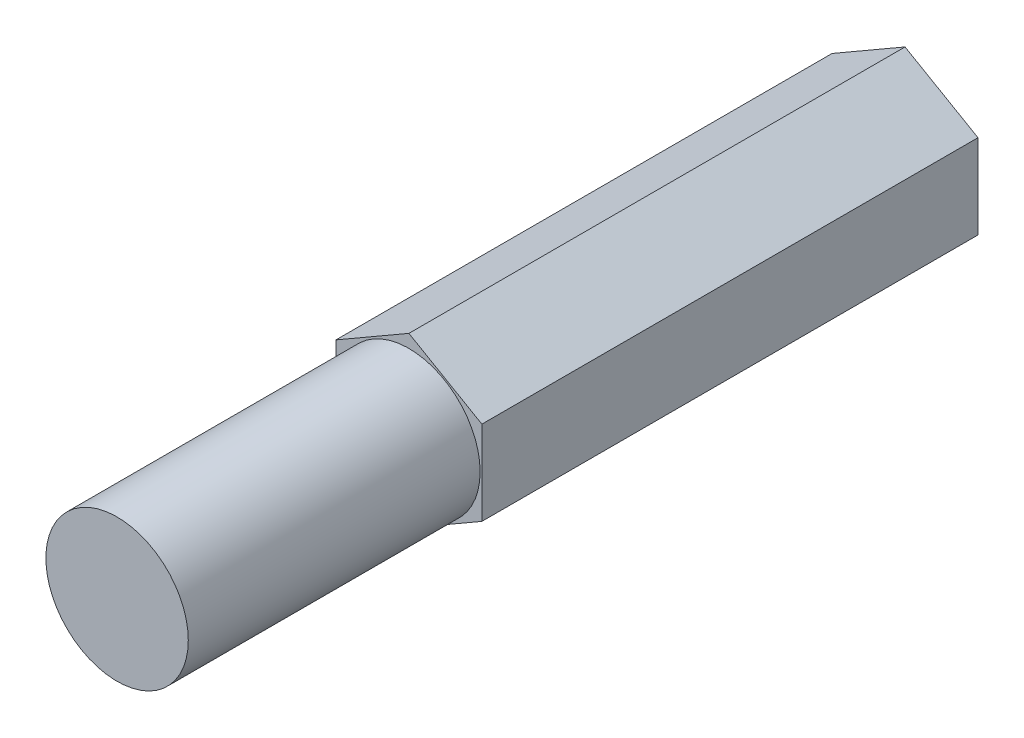
SolidWorks part; units mm, degrees
ref_plane "Front Plane" through (0, 0, 0) normal (0, 0, 1) x (1, 0, 0)
ref_plane "Top Plane" through (0, 0, 0) normal (0, 1, 0) x (1, 0, 0)
ref_plane "Right Plane" through (0, 0, 0) normal (1, 0, 0) x (0, 0, -1)
sketch "Sketch1" plane through (0, 0, 0) normal (0, 0, 1) x (1, 0, 0)
  circle A0 centre (0, 0) radius 3.0988
  dimension "D1" = 6.1976
extrude "Boss-Extrude1" add sketch "Sketch1" against normal blind 12.7
sketch "Sketch2" plane through (0, 0, -12.7) normal (0, 0, -1) x (-1, 0, 0)
  line L1 (0, 3.6662) -> (-3.175, 1.8331)
  line L2 (-3.175, 1.8331) -> (-3.175, -1.8331)
  line L3 (-3.175, -1.8331) -> (0, -3.6662)
  line L4 (0, -3.6662) -> (3.175, -1.8331)
  line L5 (3.175, -1.8331) -> (3.175, 1.8331)
  line L6 (3.175, 1.8331) -> (0, 3.6662)
  circle A0 centre (0, 0) radius 3.175 construction
  dimension "D1" = 6.35
extrude "Boss-Extrude2" add sketch "Sketch2" along normal blind 21.59
